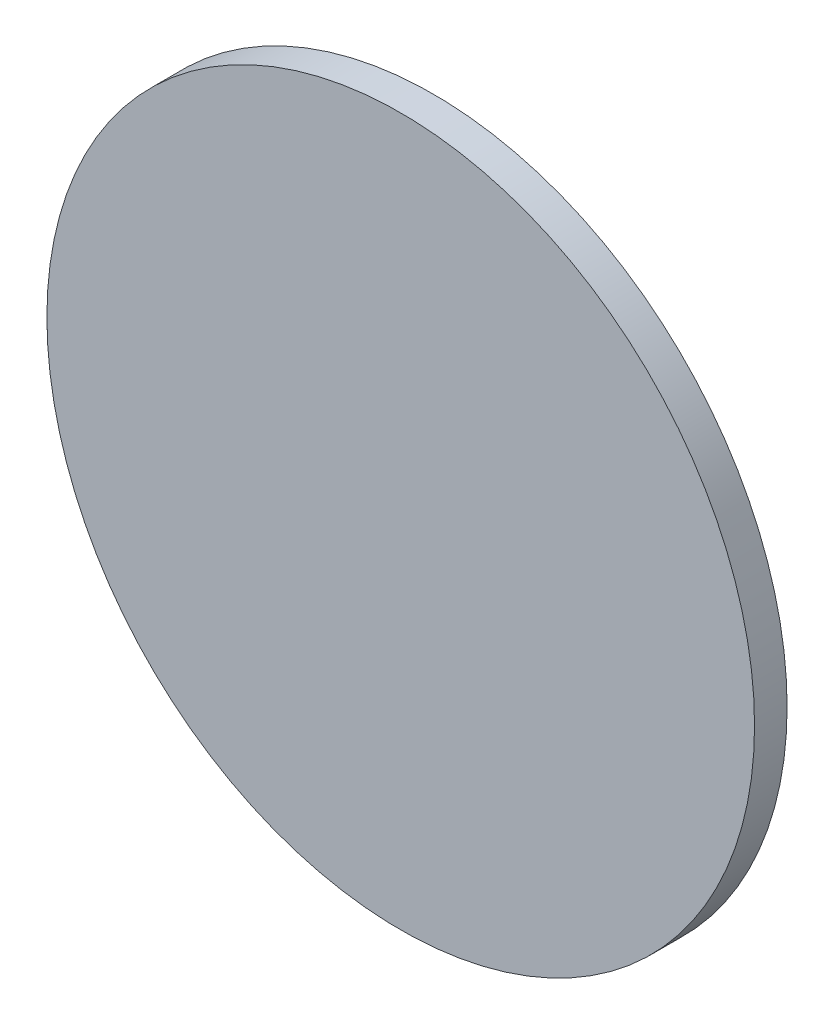
SolidWorks part; units mm, degrees
ref_plane "前视基准面" through (0, 0, 0) normal (0, 0, 1) x (1, 0, 0)
ref_plane "上视基准面" through (0, 0, 0) normal (0, 1, 0) x (1, 0, 0)
ref_plane "右视基准面" through (0, 0, 0) normal (1, 0, 0) x (0, 0, -1)
sketch "草图1" plane through (0, 0, 0) normal (0, 0, 1) x (1, 0, 0)
  circle A0 centre (217.23, 123.1265) radius 25
  dimension "D1" = 50
extrude "凸台-拉伸1" add sketch "草图1" along normal blind 2.3
